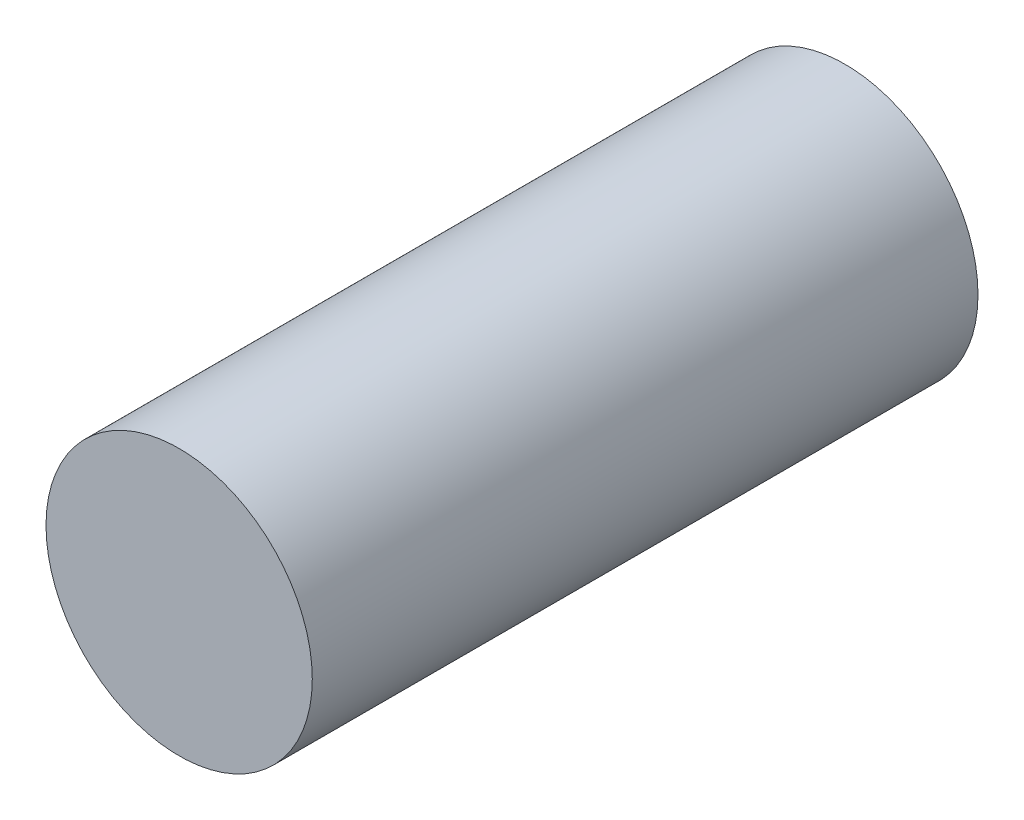
SolidWorks part; units mm, degrees
ref_plane "Alzado" through (0, 0, 0) normal (0, 0, 1) x (1, 0, 0)
ref_plane "Planta" through (0, 0, 0) normal (0, 1, 0) x (1, 0, 0)
ref_plane "Vista lateral" through (0, 0, 0) normal (1, 0, 0) x (0, 0, -1)
sketch "Croquis1" plane through (0, 0, 0) normal (0, 0, 1) x (1, 0, 0)
  circle A0 centre (0, 0) radius 5
  dimension "D1" = 10
extrude "Saliente-Extruir1" add sketch "Croquis1" along normal blind 25
